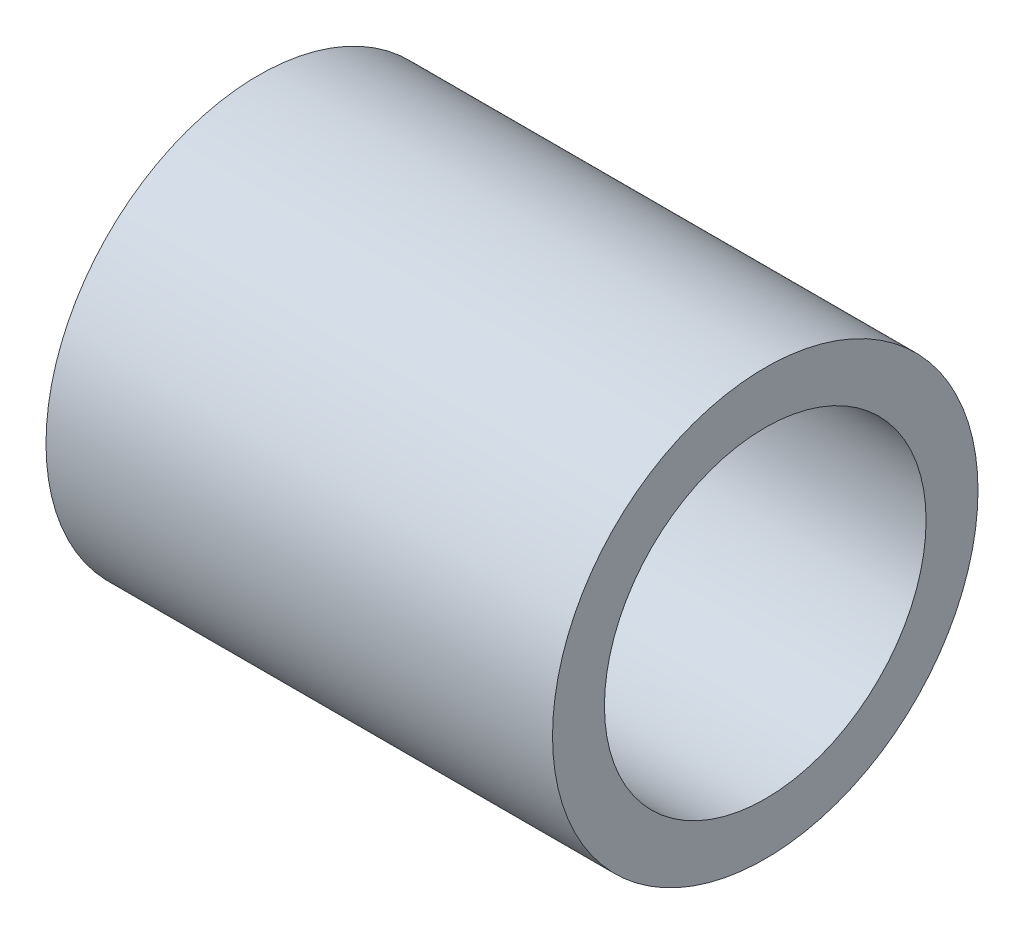
SolidWorks part; units mm, degrees
material "ABS PC"
ref_plane "Front Plane" through (0, 0, 0) normal (0, 0, 1) x (1, 0, 0)
ref_plane "Top Plane" through (0, 0, 0) normal (0, 1, 0) x (1, 0, 0)
ref_plane "Right Plane" through (0, 0, 0) normal (1, 0, 0) x (0, 0, -1)
sketch "Sketch1" plane through (0, 0, 0) normal (1, 0, 0) x (0, 0, -1)
  circle A0 centre (0, 0) radius 1.5875
  circle A1 centre (0, 0) radius 2.1
  dimension "D1" = 3.175
  dimension "D2" = 4.2
extrude "Boss-Extrude1" add sketch "Sketch1" along normal mid plane 5
